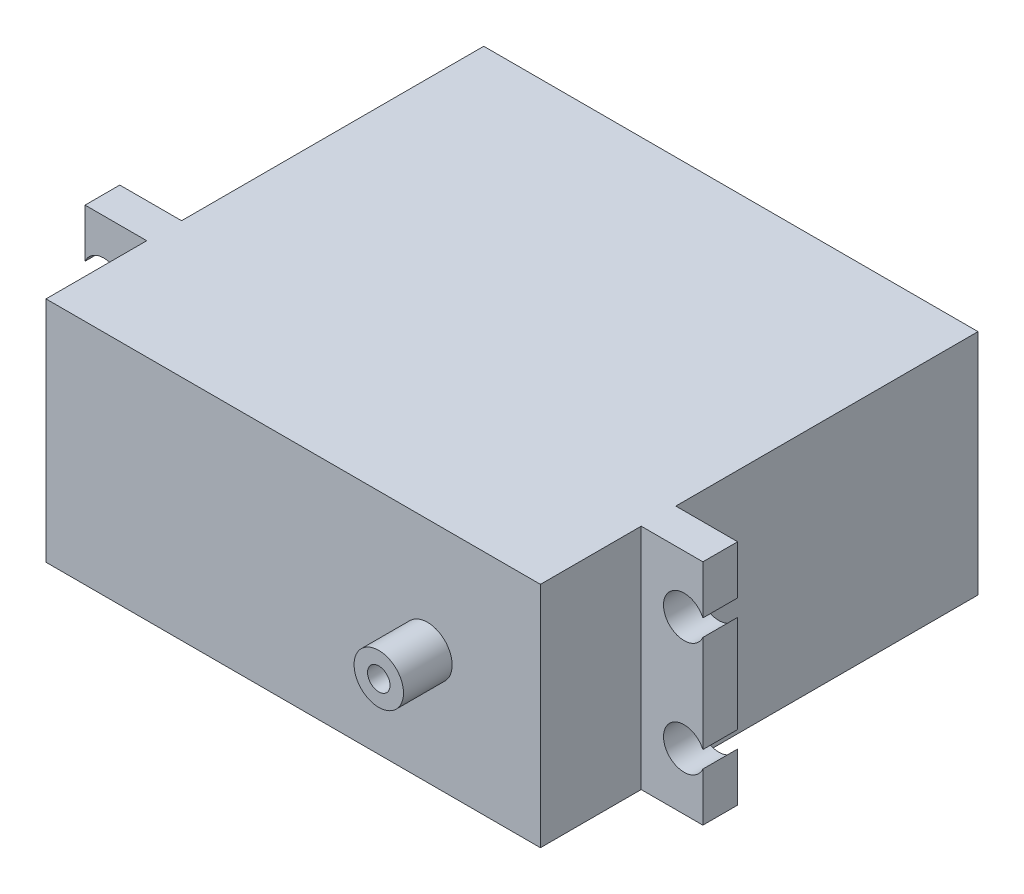
SolidWorks part; units mm, degrees
material "연성 주철"
ref_plane "정면" through (0, 0, 0) normal (0, 0, 1) x (1, 0, 0)
ref_plane "윗면" through (0, 0, 0) normal (0, 1, 0) x (1, 0, 0)
ref_plane "우측면" through (0, 0, 0) normal (1, 0, 0) x (0, 0, -1)
sketch "스케치1" plane through (0, 0, 0) normal (0, 0, 1) x (1, 0, 0)
  line L1 (33.02, -15.24) -> (-33.02, -15.24)
  line L2 (33.02, -15.24) -> (33.02, 15.24)
  line L3 (33.02, 15.24) -> (-33.02, 15.24)
  line L4 (-33.02, -15.24) -> (-33.02, 15.24)
  line L5 (33.02, -15.24) -> (-33.02, 15.24) construction
  line L6 (33.02, 15.24) -> (-33.02, -15.24) construction
  point P0 (0, 0)
  dimension "D1" = 66.04
  dimension "D2" = 30.48
extrude "보스-돌출1" add sketch "스케치1" along normal blind 40.3754
ref_plane "평면1" through (0, 0, 40.3754) normal (0, 0, 1) x (1, 0, 0)
sketch "스케치2" plane through (0, 0, 40.3754) normal (0, 0, 1) x (1, 0, 0)
  line L0 (0, 15.24) -> (0, -15.24) construction
  line L1 (41.275, -15.24) -> (-41.275, -15.24)
  line L2 (-41.275, 8.7417) -> (-41.275, 15.24)
  line L3 (-41.275, -8.7417) -> (-41.275, -15.24)
  line L4 (-41.275, 8.7417) -> (-41.275, 15.24)
  line L5 (-41.275, -8.7417) -> (-41.275, -15.24)
  line L6 (-41.275, -8.7417) -> (-41.275, -15.24)
  line L7 (41.275, 15.24) -> (-41.275, 15.24)
  line L8 (41.275, -15.24) -> (-41.275, -15.24)
  line L9 (-41.275, 8.7417) -> (-41.275, 15.24)
  line L10 (-41.275, 6.4896) -> (-41.275, -6.4896)
  line L11 (-41.275, 0) -> (41.275, 0) construction
  line L12 (41.275, -15.24) -> (-41.275, -15.24)
  line L13 (-41.275, -8.7417) -> (-41.275, -15.24)
  line L14 (-41.275, 8.7417) -> (-41.275, 15.24)
  line L15 (41.275, 8.7417) -> (41.275, 15.24)
  line L16 (41.275, -8.7417) -> (41.275, -15.24)
  line L17 (41.275, 6.4896) -> (41.275, -6.4896)
  line L18 (41.275, 8.7417) -> (41.275, 15.24)
  line L19 (41.275, -8.7417) -> (41.275, -15.24)
  line L20 (41.275, -8.7417) -> (41.275, -15.24)
  line L21 (41.275, 8.7417) -> (41.275, 15.24)
  line L22 (41.275, -8.7417) -> (41.275, -15.24)
  line L23 (41.275, 8.7417) -> (41.275, 15.24)
  line L24 (-33.02, -15.24) -> (33.02, -15.24) construction
  line L25 (33.02, 15.24) -> (-33.02, 15.24) construction
  arc A0 (-41.275, -8.7417) -> (-41.275, -6.4896) centre (-38.7661, -7.6156) ccw
  arc A1 (-41.275, -8.7417) -> (-41.275, -6.4896) centre (-38.7661, -7.6156) ccw
  arc A2 (-41.275, 8.7417) -> (-41.275, 6.4896) centre (-38.7661, 7.6156) cw
  arc A3 (41.275, 8.7417) -> (41.275, 6.4896) centre (38.7661, 7.6156) ccw
  arc A4 (-41.275, 8.7417) -> (-41.275, 6.4896) centre (-38.7661, 7.6156) cw
  arc A5 (41.275, 8.7417) -> (41.275, 6.4896) centre (38.7661, 7.6156) ccw
  arc A6 (41.275, -8.7417) -> (41.275, -6.4896) centre (38.7661, -7.6156) cw
  arc A7 (41.275, -8.7417) -> (41.275, -6.4896) centre (38.7661, -7.6156) cw
  point P0 (-0.2214, 0.7433)
  point P3 (0, 0)
  dimension "D7" = 6.4983
  dimension "D8" = 12.9791
  dimension "D9" = 6.4983
  dimension "D5" = 2.75
  dimension "D6" = 2.75
  dimension "D1" = 82.55
  dimension "D2" = 6.4983
  dimension "D3" = 12.9791
  dimension "D4" = 6.4983
  dimension "D10" = 82.55
extrude "보스-돌출11" add sketch "스케치2" along normal blind 4.64 contours L16 A6 L17 A3 L15 L7 L2 A2 L10 A0 L3 L1
ref_plane "평면2" through (0, 0, 45.0154) normal (0, 0, 1) x (1, 0, 0)
sketch "스케치3" plane through (0, 0, 45.0154) normal (0, 0, 1) x (1, 0, 0)
  line L0 (41.275, 15.24) -> (-41.275, 15.24) construction
  line L1 (33.0324, -15.24) -> (-33.0324, -15.24)
  line L2 (33.0324, -15.24) -> (33.0324, 15.24)
  line L3 (33.0324, 15.24) -> (-33.0324, 15.24)
  line L4 (-33.0324, -15.24) -> (-33.0324, 15.24)
  line L5 (33.0324, -15.24) -> (-33.0324, 15.24) construction
  line L6 (33.0324, 15.24) -> (-33.0324, -15.24) construction
  point P0 (0, 0)
  dimension "D1" = 30.48
  dimension "D2" = 66.0647
extrude "보스-돌출12" add sketch "스케치3" along normal blind 13.462
ref_plane "평면3" through (0, 0, 58.4774) normal (0, 0, 1) x (1, 0, 0)
sketch "스케치5" plane through (0, 0, 58.4774) normal (0, 0, 1) x (1, 0, 0)
  line L0 (33.0324, -15.24) -> (33.0324, 15.24) construction
  circle A0 centre (17.9325, 0) radius 1.5
  circle A1 centre (17.9325, 0) radius 3.302
  dimension "D1" = 3
  dimension "D2" = 6.604
  dimension "D3" = 15.0999
ref_plane "평면4" through (0, 0, 58.4774) normal (0, 0, 1) x (1, 0, 0)
extrude "보스-돌출13" add sketch "스케치5" along normal blind 6.5
